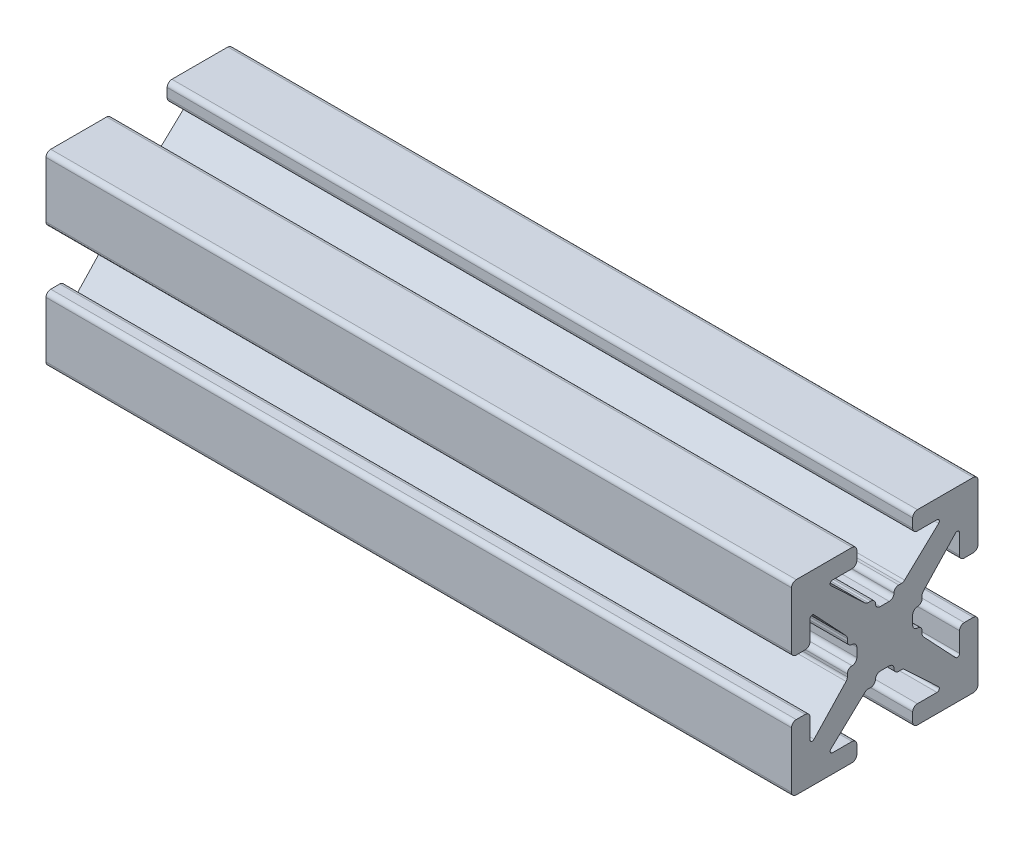
SolidWorks part; units mm, degrees
ref_plane "Front Plane" through (0, 0, 0) normal (0, 0, 1) x (1, 0, 0)
ref_plane "Top Plane" through (0, 0, 0) normal (0, 1, 0) x (1, 0, 0)
ref_plane "Right Plane" through (0, 0, 0) normal (1, 0, 0) x (0, 0, -1)
sketch "Sketch1" plane through (0, 0, 0) normal (1, 0, 0) x (0, 0, -1)
  line L0 (0, 0) -> (0, 1.4986) construction
  line L1 (-0.2413, 1.4986) -> (0.2413, 1.4986)
  line L2 (5.0038, 1.7526) -> (5.0038, 4.7498)
  line L3 (0.7493, 2.0066) -> (0.8899, 2.0066)
  line L4 (1.0639, 2.0756) -> (2.8908, 3.7937)
  line L5 (2.8038, 4.0132) -> (1.7526, 4.0132)
  line L6 (1.4986, 4.2672) -> (1.4986, 4.7498)
  line L7 (1.7526, 5.0038) -> (4.7498, 5.0038)
  line L8 (5.0038, 5.0038) -> (0, 0) construction
  line L9 (0, 0) -> (8.6271, 0) construction
  line L10 (0, 0) -> (0, 5.0038) construction
  line L11 (4.2672, 1.4986) -> (4.7498, 1.4986)
  line L12 (4.0132, 2.8038) -> (4.0132, 1.7526)
  line L13 (2.0756, 1.0639) -> (3.7937, 2.8908)
  line L14 (2.0066, 0.7493) -> (2.0066, 0.8899)
  line L15 (1.4986, -0.2413) -> (1.4986, 0.2413)
  line L16 (0, 0) -> (1.4986, 0) construction
  line L17 (-0.2413, -1.4986) -> (0.2413, -1.4986)
  line L18 (0.7493, -2.0066) -> (0.8899, -2.0066)
  line L19 (1.0639, -2.0756) -> (2.8908, -3.7937)
  line L20 (2.8038, -4.0132) -> (1.7526, -4.0132)
  line L21 (1.4986, -4.2672) -> (1.4986, -4.7498)
  line L22 (1.7526, -5.0038) -> (4.7498, -5.0038)
  line L23 (5.0038, -1.7526) -> (5.0038, -4.7498)
  line L24 (4.2672, -1.4986) -> (4.7498, -1.4986)
  line L25 (4.0132, -2.8038) -> (4.0132, -1.7526)
  line L26 (2.0756, -1.0639) -> (3.7937, -2.8908)
  line L27 (2.0066, -0.7493) -> (2.0066, -0.8899)
  line L28 (-0.7493, 2.0066) -> (-0.8899, 2.0066)
  line L29 (-1.0639, 2.0756) -> (-2.8908, 3.7937)
  line L30 (-2.8038, 4.0132) -> (-1.7526, 4.0132)
  line L31 (-1.4986, 4.2672) -> (-1.4986, 4.7498)
  line L32 (-1.7526, 5.0038) -> (-4.7498, 5.0038)
  line L33 (-5.0038, 1.7526) -> (-5.0038, 4.7498)
  line L34 (-4.2672, 1.4986) -> (-4.7498, 1.4986)
  line L35 (-4.0132, 2.8038) -> (-4.0132, 1.7526)
  line L36 (-2.0756, 1.0639) -> (-3.7937, 2.8908)
  line L37 (-2.0066, 0.7493) -> (-2.0066, 0.8899)
  line L38 (-1.4986, -0.2413) -> (-1.4986, 0.2413)
  line L39 (-2.0066, -0.7493) -> (-2.0066, -0.8899)
  line L40 (-2.0756, -1.0639) -> (-3.7937, -2.8908)
  line L41 (-4.0132, -2.8038) -> (-4.0132, -1.7526)
  line L42 (-4.2672, -1.4986) -> (-4.7498, -1.4986)
  line L43 (-5.0038, -1.7526) -> (-5.0038, -4.7498)
  line L44 (-1.7526, -5.0038) -> (-4.7498, -5.0038)
  line L45 (-1.4986, -4.2672) -> (-1.4986, -4.7498)
  line L46 (-2.8038, -4.0132) -> (-1.7526, -4.0132)
  line L47 (-1.0639, -2.0756) -> (-2.8908, -3.7937)
  line L48 (-0.7493, -2.0066) -> (-0.8899, -2.0066)
  arc A0 (2.8908, 3.7937) -> (2.8038, 4.0132) centre (2.8038, 3.8862) ccw
  arc A1 (0.4953, 1.7526) -> (0.7493, 2.0066) centre (0.7493, 1.7526) cw
  arc A2 (0.8899, 2.0066) -> (1.0639, 2.0756) centre (0.8899, 2.2606) ccw
  arc A3 (1.7526, 4.0132) -> (1.4986, 4.2672) centre (1.7526, 4.2672) cw
  arc A4 (1.4986, 4.7498) -> (1.7526, 5.0038) centre (1.7526, 4.7498) cw
  arc A5 (0.2413, 1.4986) -> (0.4953, 1.7526) centre (0.2413, 1.7526) ccw
  arc A6 (4.7498, 1.4986) -> (5.0038, 1.7526) centre (4.7498, 1.7526) ccw
  arc A7 (4.0132, 1.7526) -> (4.2672, 1.4986) centre (4.2672, 1.7526) ccw
  arc A8 (3.7937, 2.8908) -> (4.0132, 2.8038) centre (3.8862, 2.8038) cw
  arc A9 (2.0066, 0.8899) -> (2.0756, 1.0639) centre (2.2606, 0.8899) cw
  arc A10 (1.7526, 0.4953) -> (2.0066, 0.7493) centre (1.7526, 0.7493) ccw
  arc A11 (1.4986, 0.2413) -> (1.7526, 0.4953) centre (1.7526, 0.2413) cw
  arc A12 (0.2413, -1.4986) -> (0.4953, -1.7526) centre (0.2413, -1.7526) cw
  arc A13 (0.4953, -1.7526) -> (0.7493, -2.0066) centre (0.7493, -1.7526) ccw
  arc A14 (0.8899, -2.0066) -> (1.0639, -2.0756) centre (0.8899, -2.2606) cw
  arc A15 (2.8908, -3.7937) -> (2.8038, -4.0132) centre (2.8038, -3.8862) cw
  arc A16 (1.7526, -4.0132) -> (1.4986, -4.2672) centre (1.7526, -4.2672) ccw
  arc A17 (1.4986, -4.7498) -> (1.7526, -5.0038) centre (1.7526, -4.7498) ccw
  arc A18 (4.7498, -1.4986) -> (5.0038, -1.7526) centre (4.7498, -1.7526) cw
  arc A19 (4.0132, -1.7526) -> (4.2672, -1.4986) centre (4.2672, -1.7526) cw
  arc A20 (3.7937, -2.8908) -> (4.0132, -2.8038) centre (3.8862, -2.8038) ccw
  arc A21 (2.0066, -0.8899) -> (2.0756, -1.0639) centre (2.2606, -0.8899) ccw
  arc A22 (1.7526, -0.4953) -> (2.0066, -0.7493) centre (1.7526, -0.7493) cw
  arc A23 (1.4986, -0.2413) -> (1.7526, -0.4953) centre (1.7526, -0.2413) ccw
  arc A24 (-0.2413, 1.4986) -> (-0.4953, 1.7526) centre (-0.2413, 1.7526) cw
  arc A25 (-0.4953, 1.7526) -> (-0.7493, 2.0066) centre (-0.7493, 1.7526) ccw
  arc A26 (-0.8899, 2.0066) -> (-1.0639, 2.0756) centre (-0.8899, 2.2606) cw
  arc A27 (-2.8908, 3.7937) -> (-2.8038, 4.0132) centre (-2.8038, 3.8862) cw
  arc A28 (-1.7526, 4.0132) -> (-1.4986, 4.2672) centre (-1.7526, 4.2672) ccw
  arc A29 (-1.4986, 4.7498) -> (-1.7526, 5.0038) centre (-1.7526, 4.7498) ccw
  arc A30 (-4.7498, 1.4986) -> (-5.0038, 1.7526) centre (-4.7498, 1.7526) cw
  arc A31 (-4.0132, 1.7526) -> (-4.2672, 1.4986) centre (-4.2672, 1.7526) cw
  arc A32 (-3.7937, 2.8908) -> (-4.0132, 2.8038) centre (-3.8862, 2.8038) ccw
  arc A33 (-2.0066, 0.8899) -> (-2.0756, 1.0639) centre (-2.2606, 0.8899) ccw
  arc A34 (-1.7526, 0.4953) -> (-2.0066, 0.7493) centre (-1.7526, 0.7493) cw
  arc A35 (-1.4986, 0.2413) -> (-1.7526, 0.4953) centre (-1.7526, 0.2413) ccw
  arc A36 (-1.4986, -0.2413) -> (-1.7526, -0.4953) centre (-1.7526, -0.2413) cw
  arc A37 (-1.7526, -0.4953) -> (-2.0066, -0.7493) centre (-1.7526, -0.7493) ccw
  arc A38 (-2.0066, -0.8899) -> (-2.0756, -1.0639) centre (-2.2606, -0.8899) cw
  arc A39 (-3.7937, -2.8908) -> (-4.0132, -2.8038) centre (-3.8862, -2.8038) cw
  arc A40 (-4.0132, -1.7526) -> (-4.2672, -1.4986) centre (-4.2672, -1.7526) ccw
  arc A41 (-4.7498, -1.4986) -> (-5.0038, -1.7526) centre (-4.7498, -1.7526) ccw
  arc A42 (-1.4986, -4.7498) -> (-1.7526, -5.0038) centre (-1.7526, -4.7498) cw
  arc A43 (-1.7526, -4.0132) -> (-1.4986, -4.2672) centre (-1.7526, -4.2672) cw
  arc A44 (-2.8908, -3.7937) -> (-2.8038, -4.0132) centre (-2.8038, -3.8862) ccw
  arc A45 (-0.8899, -2.0066) -> (-1.0639, -2.0756) centre (-0.8899, -2.2606) ccw
  arc A46 (-0.4953, -1.7526) -> (-0.7493, -2.0066) centre (-0.7493, -1.7526) cw
  arc A47 (-0.2413, -1.4986) -> (-0.4953, -1.7526) centre (-0.2413, -1.7526) ccw
  arc A48 (-4.7498, 5.0038) -> (-5.0038, 4.7498) centre (-4.7498, 4.7498) ccw
  arc A49 (-5.0038, -4.7498) -> (-4.7498, -5.0038) centre (-4.7498, -4.7498) ccw
  arc A50 (4.7498, -5.0038) -> (5.0038, -4.7498) centre (4.7498, -4.7498) ccw
  arc A51 (4.7498, 5.0038) -> (5.0038, 4.7498) centre (4.7498, 4.7498) cw
  point P14 (3.1242, 4.0132)
  point P19 (0.9906, 2.0066)
  point P150 (0, -1.4986)
  point P152 (-5.0038, 5.0038)
  point P155 (-5.0038, -5.0038)
  point P158 (5.0038, -5.0038)
  dimension "D10" = 0.127
  dimension "D11" = 0.254
  dimension "D2" = 0.254
  dimension "D1" = 10.0076
  dimension "D3" = 2.9972
  dimension "D4" = 0.508
  dimension "D5" = 2.9972
  dimension "D6" = 0.9906
  dimension "D7" = 1.6256
  dimension "D8" = 1.9812
  dimension "D9" = 0.9906
extrude "Boss.-Extru.1" add sketch "Sketch1" along normal blind 40
